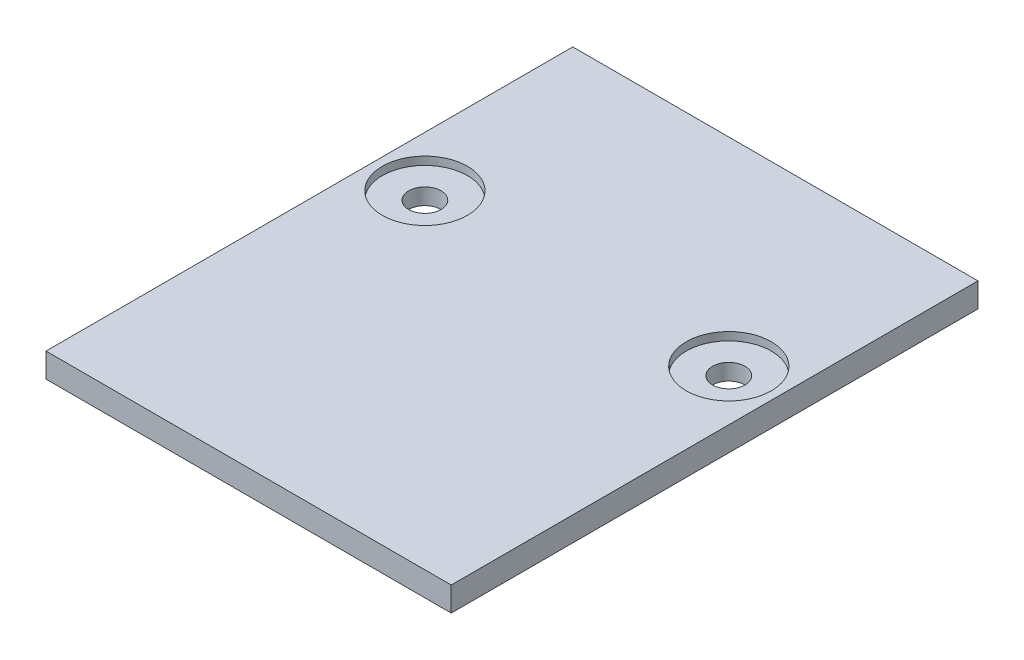
SolidWorks part; units mm, degrees
material "Plain Carbon Steel"
ref_plane "Front Plane" through (0, 0, 0) normal (0, 0, 1) x (1, 0, 0)
ref_plane "Top Plane" through (0, 0, 0) normal (0, 1, 0) x (1, 0, 0)
ref_plane "Right Plane" through (0, 0, 0) normal (1, 0, 0) x (0, 0, -1)
sketch "Sketch1" plane through (0, 0, 0) normal (0, 1, 0) x (1, 0, 0)
  line L1 (-50, -65) -> (50, -65)
  line L2 (-50, -65) -> (-50, 65)
  line L3 (-50, 65) -> (50, 65)
  line L4 (50, -65) -> (50, 65)
  line L5 (-50, -65) -> (50, 65) construction
  line L6 (-50, 65) -> (50, -65) construction
  point P0 (0, 0)
  dimension "D1" = 130
  dimension "D2" = 100
extrude "Boss-Extrude1" add sketch "Sketch1" along normal blind 6
sketch "Sketch2" [suppressed] plane through (0, 0, 0) normal (0, -1, 0) x (1, 0, 0)
  line L0 (-50, 65) -> (50, 65) construction
  circle A0 centre (0, 50) radius 11.5
  dimension "D1" = 23
  dimension "D2" = 15
extrude "Cut-Extrude1" [suppressed] cut sketch "Sketch2" against normal blind 2
sketch "Sketch3" plane through (0, 6, 0) normal (0, 1, 0) x (1, 0, 0)
  line L0 (50, 65) -> (-50, 65) construction
  circle A0 centre (-37.5, 16) radius 4
  circle A1 centre (37.5, 16) radius 4
  dimension "D1" = 8
  dimension "D2" = 8
  dimension "D6" = 37.5
  dimension "D3" = 49
  dimension "D4" = 49
  dimension "D5" = 75
extrude "Cut-Extrude2" cut sketch "Sketch3" against normal through all
sketch "Sketch4" plane through (0, 6, 0) normal (0, 1, 0) x (1, 0, 0)
  circle A0 centre (37.5, 16) radius 10.5
  circle A1 centre (-37.5, 16) radius 10.5
  dimension "D1" = 21
  dimension "D2" = 21
extrude "Cut-Extrude3" cut sketch "Sketch4" against normal blind 2
sketch "Sketch5" [suppressed] plane through (0, 2, 0) normal (0, -1, 0) x (1, 0, 0)
  circle A0 centre (0, 50.3) radius 7.5
  dimension "D1" = 15
extrude "Cut-Extrude4" [suppressed] cut sketch "Sketch5" against normal through all
